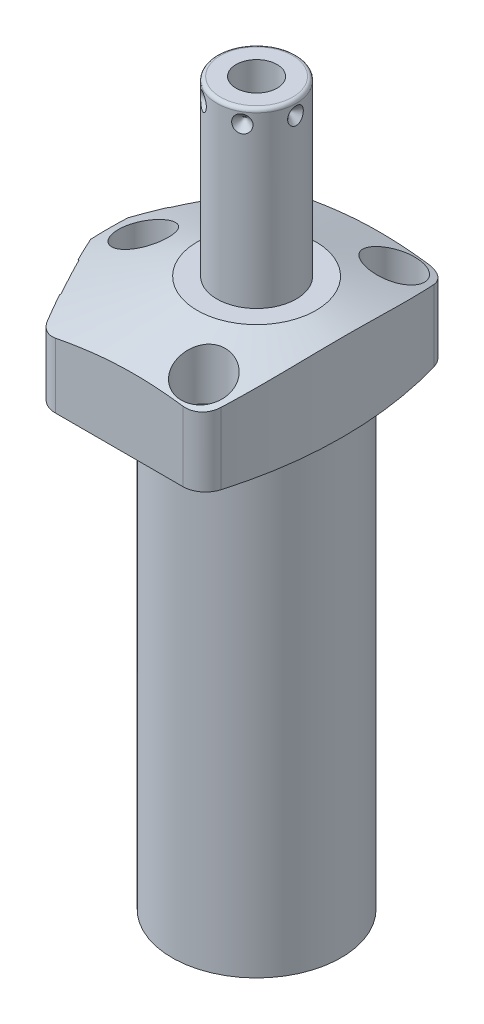
SolidWorks part; units mm, degrees
material "Alloy Steel"
ref_plane "Front Plane" through (0, 0, 0) normal (0, 0, 1) x (1, 0, 0)
ref_plane "Top Plane" through (0, 0, 0) normal (0, 1, 0) x (1, 0, 0)
ref_plane "Right Plane" through (0, 0, 0) normal (1, 0, 0) x (0, 0, -1)
sketch "Sketch1" plane through (0, 0, 0) normal (0, 0, 1) x (1, 0, 0)
  line L0 (44.45, 0) -> (44.45, 26.9748)
  line L1 (44.45, 26.9748) -> (0, 26.9748)
  line L2 (0, 26.9748) -> (0, -126.5682)
  line L3 (0, -126.5682) -> (23.6855, -126.5682)
  line L4 (23.6855, -126.5682) -> (23.6855, 0)
  line L5 (23.6855, 0) -> (44.45, 0)
  line L6 (0, 32.531) -> (0, -89.7065) construction
  dimension "D1" = 153.543
  dimension "D2" = 26.9748
  dimension "D3" = 88.9
  dimension "D4" = 47.371
revolve "Revolve1" add sketch "Sketch1" angle 360 about L6
sketch "Sketch2" plane through (0, 0, 0) normal (0, -1, 0) x (1, 0, 0)
  line L0 (-28.1296, -34.417) -> (28.1296, -34.417)
  line L2 (28.1296, 34.417) -> (-28.1296, 34.417)
  line L3 (-0.6196, 0) -> (52.8973, 0) construction
  arc A0 (-28.1296, -34.417) -> (28.1296, -34.417) centre (0, 0) ccw
  circle A1 centre (0, 0) radius 44.45
  arc A2 (28.1296, 34.417) -> (-28.1296, 34.417) centre (0, 0) ccw
  point P4 (0, 0)
  dimension "D1" = 68.834
  dimension "D2" = 0
extrude "Cut-Extrude1" cut sketch "Sketch2" against normal up to next
sketch "Sketch3" plane through (0, 0, 0) normal (0, -1, 0) x (1, 0, 0)
  line L0 (-25.7429, -34.417) -> (-44.0427, 0)
  line L1 (-44.0427, 0) -> (-25.7429, 34.417)
  line L2 (-39.4859, -20.995) -> (73.8214, 39.2515) construction
  line L3 (0, 0) -> (-44.0427, 0) construction
  line L6 (28.1296, 34.417) -> (-28.1296, 34.417)
  line L7 (-28.1296, -34.417) -> (28.1296, -34.417)
  line L8 (-25.7429, 34.417) -> (-28.1296, 34.417)
  line L9 (-28.1296, -34.417) -> (-25.7429, -34.417)
  arc A2 (28.1296, -34.417) -> (28.1296, 34.417) centre (0, 0) ccw
  arc A3 (-28.1296, 34.417) -> (-28.1296, -34.417) centre (0, 0) ccw
  arc A5 (-28.1296, 34.417) -> (-28.1296, -34.417) centre (0, 0) ccw
  dimension "D1" = 28
  dimension "D2" = 38.8874
  dimension "D3" = 0
extrude "Cut-Extrude2" cut sketch "Sketch3" against normal up to next
sketch "S2D0002" plane through (0, 26.9748, 0) normal (0, -1, 0) x (-1, 0, 0)
  line L0 (41.275, 98.1689) -> (41.275, -98.1689)
  arc A0 (41.275, 98.1689) -> (41.275, -98.1689) centre (82.2452, 0) ccw
  dimension "D3" = 106.3752
  dimension "D1" = 82.2452
  dimension "D2" = 41.275
extrude "Cut-Extrude3" cut sketch "S2D0002" along normal up to surface (26.9748 mm away) flip side to cut up to face at (-4.5898, 0, 0)
fillet "Fillet1" radius 6.35 2 edges at (18.4084, 13.4874, 34.417) (18.4084, 13.4874, -34.417)
fillet "Fillet2" radius 6.35 1 edges at (-25.7429, 13.4874, 34.417)
fillet "Fillet3" radius 6.35 1 edges at (-25.7429, 13.4874, -34.417)
sketch "Sketch5" plane through (0, 0, 0) normal (0, 0, 1) x (1, 0, 0)
  line L0 (-16.637, 26.9748) -> (-47.625, 15.6961)
  line L1 (0, 7.6649) -> (0, 27.5963) construction
  line L3 (13.7615, 26.9748) -> (-21.9274, 26.9748) construction
  line L4 (-16.637, 26.9748) -> (-47.625, 26.9748)
  line L5 (-47.625, 26.9748) -> (-47.625, 15.6961)
  dimension "D1" = 33.274
  dimension "D2" = 20
  dimension "D3" = 47.625
revolve "Cut-Revolve1" cut sketch "Sketch5" angle 360 about L1
ref_plane "Plane6" through (-34.1113, 10.287, -18.1373) normal (0, 1, 0) x (0.4695, 0, -0.8829)
sketch "Sketch6" plane through (-34.1113, 10.287, -18.1373) normal (0, 1, 0) x (0.4695, 0, -0.8829)
  line L0 (0, 0) -> (6.1849, 0)
  line L1 (6.1849, 0) -> (5.6423, -2.5527)
  line L2 (5.6423, -2.5527) -> (4.9784, -3.2166)
  line L3 (4.9784, -3.2166) -> (4.9784, -15.748)
  line L4 (4.9784, -15.748) -> (0, -15.748)
  line L5 (0, -15.748) -> (0, 0)
  line L6 (0, -16.5354) -> (0, 0.7874) construction
  dimension "D1" = 15.748
revolve "Cut-Revolve2" cut sketch "Sketch6" angle 360 about L6
ref_plane "Plane7" through (-34.1113, 10.287, 18.1373) normal (0, 1, 0) x (-0.4695, 0, -0.8829)
sketch "Sketch7" plane through (-34.1113, 10.287, 18.1373) normal (0, 1, 0) x (-0.4695, 0, -0.8829)
  line L0 (0, 0) -> (6.1849, 0)
  line L1 (6.1849, 0) -> (5.6423, -2.5527)
  line L2 (5.6423, -2.5527) -> (4.9784, -3.2166)
  line L3 (4.9784, -3.2166) -> (4.9784, -15.748)
  line L4 (4.9784, -15.748) -> (0, -15.748)
  line L5 (0, -15.748) -> (0, 0)
  line L6 (0, -16.5354) -> (0, 0.7874) construction
  dimension "D1" = 15.748
revolve "Cut-Revolve3" cut sketch "Sketch7" angle 360 about L6
ref_plane "Plane9" through (-13.4874, 2.667, 26.5938) normal (0, 0, 1) x (-1, 0, 0)
sketch "Sketch9" plane through (-13.4874, 2.667, 26.5938) normal (0, 0, 1) x (-1, 0, 0)
  line L0 (5.5626, 0) -> (10.1092, 0)
  line L1 (10.1092, 0) -> (9.6692, -2.0701)
  line L2 (9.6692, -2.0701) -> (9.017, -2.7223)
  line L3 (9.017, -2.7223) -> (9.017, -12.573)
  line L4 (9.017, -12.573) -> (5.5626, -12.573)
  line L5 (5.5626, -12.573) -> (5.5626, 0)
  line L6 (5.5626, -13.2017) -> (5.5626, 0.6287) construction
  line L7 (8.44, 2.667) -> (-27.2489, 2.667) construction
  dimension "D1" = 12.573
  dimension "D2" = 15.24
  dimension "D3" = 19.05
  dimension "D4" = 12
  dimension "D5" = 45
  dimension "D6" = 2.0701
  dimension "D7" = 9.0932
  dimension "D8" = 6.9088
revolve "Cut-Revolve5" cut sketch "Sketch9" angle 360 about L6
sketch "Sketch17" plane through (-34.3355, 0, 18.2565) normal (-0.8829, 0, 0.4695) x (0.4695, 0, 0.8829)
  circle A0 centre (0, 10.287) radius 10.4775
  dimension "D1" = 20.955
extrude "Cut-Extrude4" cut sketch "Sketch17" against normal blind 0.254
sketch "Sketch18" plane through (0, 0, 0) normal (0, -1, 0) x (1, 0, 0)
  circle A0 centre (-19.05, 26.5938) radius 5.5626
  dimension "D1" = 11.1252
extrude "Cut-Extrude5" cut sketch "Sketch18" against normal blind 2.667
mirror "Mirror1" about plane through (0, 0, 0) normal (0, 0, 1) of "Cut-Revolve5", "Cut-Extrude4", "Cut-Extrude5"
sketch "Sketch10" plane through (0, 0, 0) normal (1, 0, 0) x (0, 0, -1)
  line L0 (0, 26.9748) -> (-11.1125, 26.9748)
  line L1 (-11.1125, 26.9748) -> (-11.1125, 74.4474)
  line L2 (-10.0965, 75.4634) -> (0, 75.4634)
  line L3 (0, 75.4634) -> (0, 26.9748)
  line L4 (0, 14.3517) -> (0, 66.7398) construction
  line L5 (16.637, 26.9748) -> (-16.637, 26.9748) construction
  line L6 (-29.8488, 0) -> (29.8488, 0) construction
  arc A0 (-10.0965, 75.4634) -> (-11.1125, 74.4474) centre (-10.0965, 74.4474) ccw
  dimension "D2" = 1.016
  dimension "D1" = 75.4634
  dimension "D3" = 22.225
revolve "Revolve2" add sketch "Sketch10" angle 360 about L4
sketch "S2D0001" plane through (0, 0, 0) normal (0, 0, 1) x (1, 0, 0)
  line L0 (5.7531, 75.4634) -> (5.7531, 58.4454)
  line L1 (5.7531, 58.4454) -> (0, 54.9886)
  line L2 (5.7531, 75.4634) -> (0, 75.4634)
  line L3 (0, 75.4634) -> (0, 54.9886)
  line L4 (0, -27.7363) -> (0, 1.0237) construction
  line L5 (10.0965, 75.4634) -> (-10.0965, 75.4634) construction
  dimension "D1" = 11.5062
  dimension "D2" = 17.018
  dimension "D3" = 59
revolve "Cut-Revolve6" cut sketch "S2D0001" angle 360 about L4
sketch "Sketch14" plane through (-13.4874, 0, 26.5938) normal (0, 0, -1) x (-1, 0, 0)
  line L0 (11.0236, 2.667) -> (11.0236, 0.9398)
  line L1 (11.0236, 0.9398) -> (10.8642, 0.9398)
  line L2 (8.2296, 0.4318) -> (8.2296, 0.127)
  line L3 (8.2296, 0.127) -> (7.1501, 0.127)
  line L4 (7.1501, 0.127) -> (7.1501, 10.6172)
  line L5 (7.1501, 10.6172) -> (8.8138, 10.6172)
  line L6 (8.8138, 10.6172) -> (8.8138, 2.667)
  line L7 (8.8138, 2.667) -> (11.0236, 2.667)
  line L8 (8.7376, 0.9398) -> (9.405, 0.9398)
  line L9 (5.5626, -1.0109) -> (5.5626, 11.1709) construction
  arc A0 (8.7376, 0.9398) -> (8.2296, 0.4318) centre (8.7376, 0.4318) ccw
  arc A1 (9.405, 0.9398) -> (10.8642, 0.9398) centre (10.1346, 0.4318) ccw
  dimension "D5" = 0.889
  dimension "D1" = 2.54
  dimension "D2" = 7.9502
  dimension "D3" = 3.175
  dimension "D4" = 10.922
  dimension "D6" = 9.144
  dimension "D7" = 19.05
  dimension "D8" = 0.508
  dimension "D9" = 0.8128
revolve "Revolve3" add sketch "Sketch14" angle 360 about L9
ref_plane "Plane14" through (-11.1125, 60.8838, 0) normal (0, 0, 1) x (0, 1, 0)
sketch "Sketch15" plane through (-11.1125, 60.8838, 0) normal (0, 0, 1) x (0, 1, 0)
  line L0 (10.6172, 0) -> (13.0302, 0)
  line L1 (13.0302, 0) -> (10.6172, -2.413)
  line L2 (10.6172, 0) -> (10.6172, -2.413)
  line L3 (10.6172, -5.1094) -> (10.6172, 0.1207) construction
  line L4 (13.5636, 0) -> (-33.909, 0) construction
  line L5 (14.5796, -21.209) -> (14.5796, -1.016) construction
  dimension "D1" = 3.9624
  dimension "D2" = 4.826
  dimension "D3" = 45
revolve "Cut-Revolve7" cut sketch "Sketch15" angle 360 about L3
pattern_circular "CirPattern1" count 6 over 360 about axis through (0, 14.3517, 0) along (0, -1, 0) of "Cut-Revolve7"
hole_wizard "Hole1" positions "Sketch20" profile "Sketch19" legacy end condition up to next
sketch "Sketch20" plane through (0, 26.9748, 0) normal (0, 1, 0) x (-1, 0, 0)
  line L0 (0, 0) -> (47.6205, 0) construction
  line L1 (0, 0) -> (0, 38.9977) construction
  point P0 (-11.8872, -26.67)
  point P10 (31.75, 0)
  point P14 (-11.8872, 26.67)
  dimension "D1" = 11.8872
  dimension "D2" = 26.67
  dimension "D3" = 31.75
sketch "Sketch19" plane through (11.8872, 26.9748, -26.67) normal (1, 0, 0) x (0, 0, 1)
  line L0 (0, 0) -> (0, 26.9748)
  line L1 (0, 26.9748) -> (4.3688, 26.9748)
  line L2 (4.3688, 26.9748) -> (4.3688, 16.6624)
  line L3 (4.3688, 16.6624) -> (6.9977, 16.6624)
  line L4 (6.9977, 16.6624) -> (6.9977, 0)
  line L5 (6.9977, 0) -> (0, 0)
  line L6 (0, 110) -> (0, -10) construction
  dimension "Diameter" = 8.7376
  dimension "Depth" = 26.9748
  dimension "C-Bore Diameter" = 13.9954
  dimension "C-Bore Depth" = 16.6624
mirror "Mirror2" about plane through (0, 0, 0) normal (0, 0, 1) of "Revolve3"
